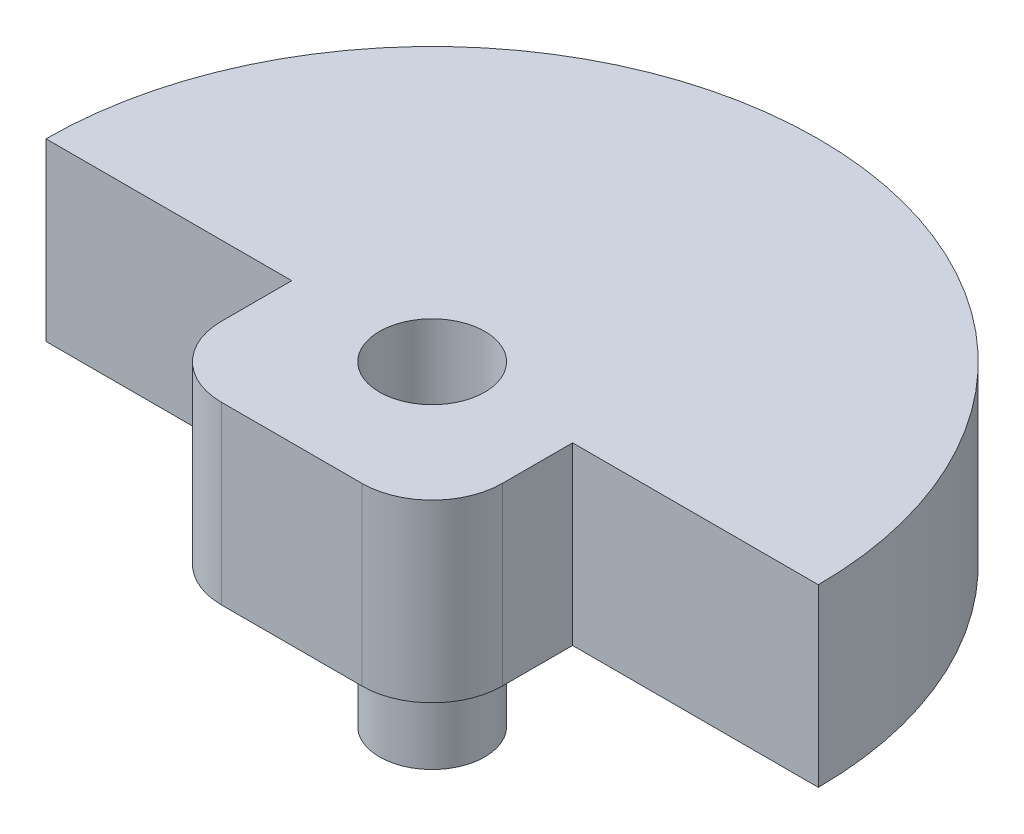
SolidWorks part; units mm, degrees
ref_plane "Front Plane" through (0, 0, 0) normal (0, 0, 1) x (1, 0, 0)
ref_plane "Top Plane" through (0, 0, 0) normal (0, 1, 0) x (1, 0, 0)
ref_plane "Right Plane" through (0, 0, 0) normal (1, 0, 0) x (0, 0, -1)
sketch "Sketch2" plane through (0, 0, 0) normal (0, 1, 0) x (1, 0, 0)
  circle A0 centre (0, 0) radius 0.375
  dimension "D1" = 0.75
extrude "Boss-Extrude1" add sketch "Sketch2" along normal blind 1 contours A0
sketch "Sketch3" plane through (0, 1, 0) normal (0, 1, 0) x (1, 0, 0)
  line L0 (-2.75, 0) -> (2.75, 0)
  line L2 (-1, 0) -> (1, 0)
  line L3 (-1, 0) -> (-1, -1)
  line L4 (-1, -1) -> (1, -1)
  line L5 (1, 0) -> (1, -1)
  circle A0 centre (0, 0) radius 2.75
  circle M2 centre (0, 0) radius 0.375
  dimension "D1" = 5.5
  dimension "D2" = 1
  dimension "D3" = 2
extrude "Boss-Extrude2" add sketch "Sketch3" along normal blind 1.25 separate body contours L0 A0 M2 | L5 L0 L3 L4 M2
fillet "Fillet1" radius 0.5 2 edges at (-1, 1.625, 1) (1, 1.625, 1)
